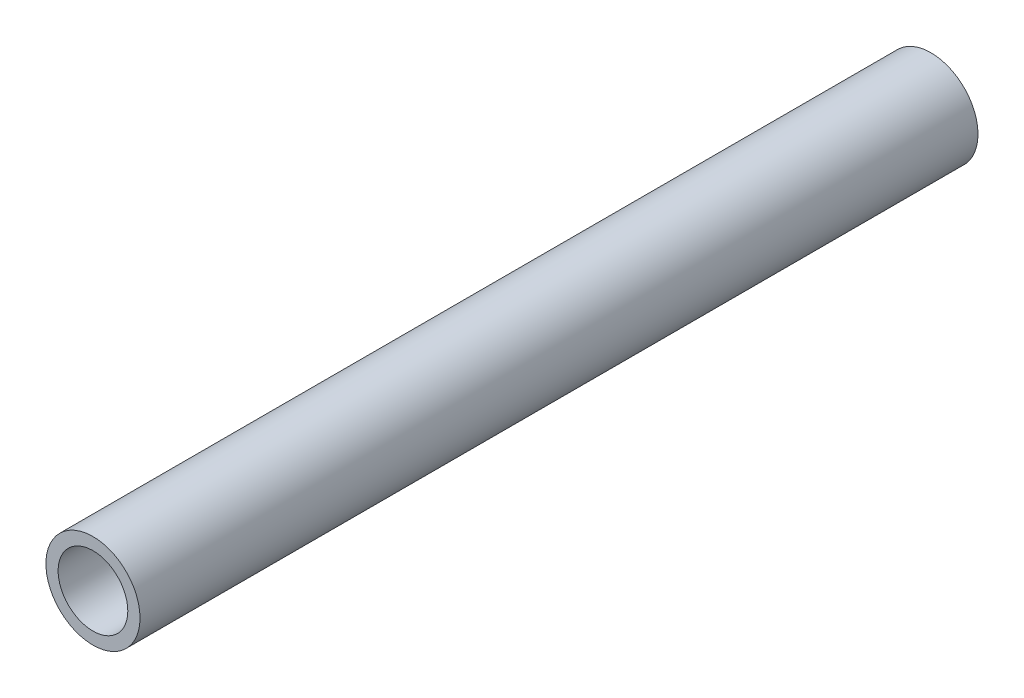
SolidWorks part; units mm, degrees
ref_plane "Front Plane" through (0, 0, 0) normal (0, 0, 1) x (1, 0, 0)
ref_plane "Top Plane" through (0, 0, 0) normal (0, 1, 0) x (1, 0, 0)
ref_plane "Right Plane" through (0, 0, 0) normal (1, 0, 0) x (0, 0, -1)
sketch "Sketch1" plane through (0, 0, 0) normal (0, 0, 1) x (1, 0, 0)
  circle A0 centre (0, 0) radius 10.668
  dimension "Pipe OD" = 21.336
extrude "Extrude-Thin1" add sketch "Sketch1" along normal mid plane 190 thin thin type one direction reverse wall 2.7686
